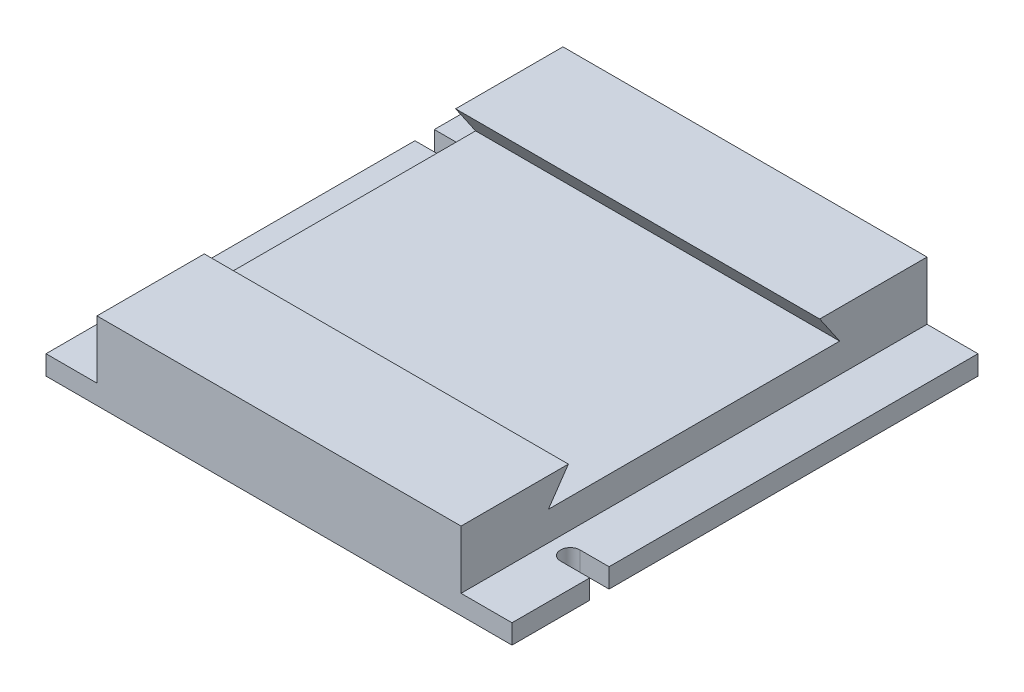
SolidWorks part; units mm, degrees
ref_plane "Спереди" through (0, 0, 0) normal (0, 0, 1) x (1, 0, 0)
ref_plane "Сверху" through (0, 0, 0) normal (0, 1, 0) x (1, 0, 0)
ref_plane "Справа" through (0, 0, 0) normal (1, 0, 0) x (0, 0, -1)
sketch "Эскиз1" plane through (0, 0, 0) normal (1, 0, 0) x (0, 0, -1)
  line L0 (-120, 0) -> (120, 0)
  line L1 (120, 0) -> (120, 40)
  line L6 (120, 40) -> (64.72, 40)
  line L7 (64.72, 40) -> (75, 25)
  line L8 (75, 25) -> (-75, 25)
  line L9 (0, 71.4806) -> (0, -37.2573) construction
  line L10 (-64.72, 40) -> (-75, 25)
  line L11 (-120, 40) -> (-64.72, 40)
  line L16 (-120, 0) -> (-120, 40)
  point P19 (0, 25)
  point P26 (0, 0)
  dimension "D1" = 120
  dimension "D2" = 40
extrude "Бобышка-Вытянуть1" add sketch "Эскиз1" along normal blind 240
sketch "Эскиз2" plane through (0, 0, 0) normal (0, -1, 0) x (1, 0, 0)
  line L5 (240, 80) -> (240, 70)
  line L6 (240, 120) -> (240, -120) construction
  line L7 (240, 70) -> (225, 70)
  line L9 (225, 80) -> (240, 80)
  line L10 (0, 0) -> (240, 0) construction
  line L11 (0, -80) -> (0, -70)
  line L12 (0, -70) -> (15, -70)
  line L13 (15, -80) -> (0, -80)
  arc A0 (225, 80) -> (225, 70) centre (225, 75) ccw
  arc A1 (15, -80) -> (15, -70) centre (15, -75) ccw
  point P9 (120, 0)
  point P19 (120, 0)
  dimension "D1" = 2
extrude "Вырез-Вытянуть1" cut sketch "Эскиз2" against normal through all
sketch "Эскиз3" plane through (0, 40, 0) normal (0, 1, 0) x (1, 0, 0)
  line L1 (0, 120) -> (26.2453, 120)
  line L2 (0, 120) -> (0, -120)
  line L3 (0, -120) -> (26.2453, -120)
  line L4 (26.2453, 120) -> (26.2453, -120)
  line L5 (120, 120) -> (120, -120) construction
  line L7 (213.7547, 120) -> (213.7547, -120)
  line L8 (240, -120) -> (213.7547, -120)
  line L9 (240, 120) -> (240, -120)
  line L10 (240, 120) -> (213.7547, 120)
extrude "Вырез-Вытянуть2" cut sketch "Эскиз3" against normal blind 30
